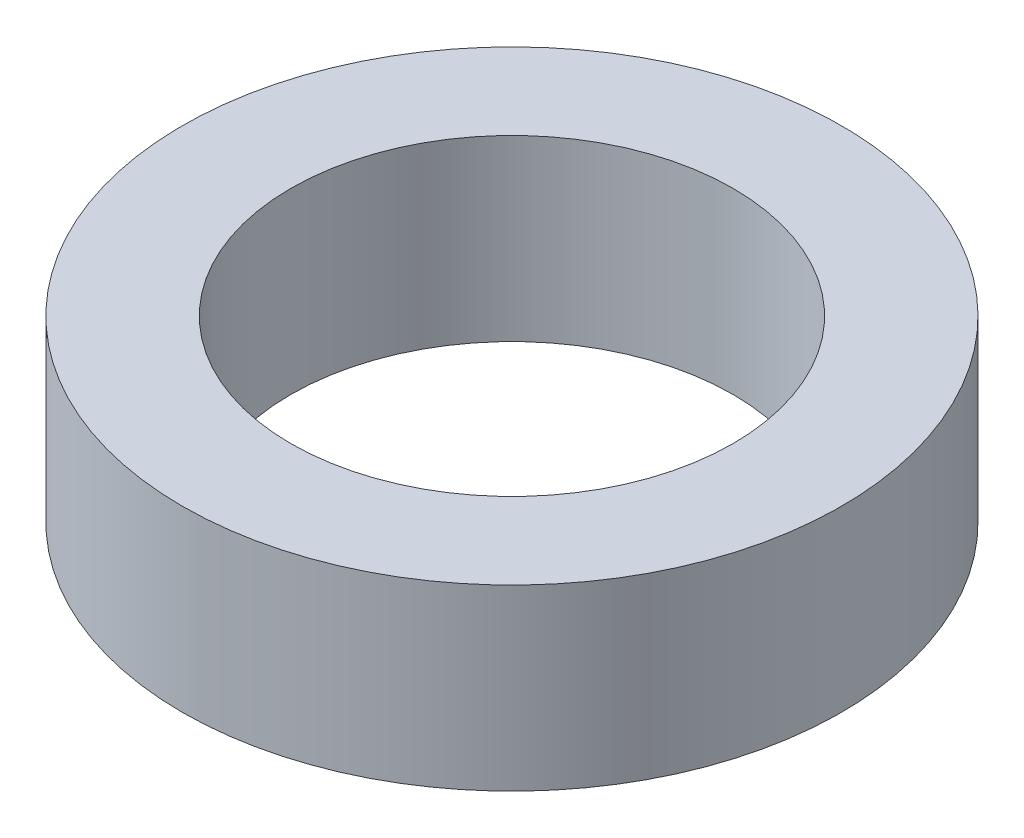
SolidWorks part; units mm, degrees
ref_plane "Front Plane" through (0, 0, 0) normal (0, 0, 1) x (1, 0, 0)
ref_plane "Top Plane" through (0, 0, 0) normal (0, 1, 0) x (1, 0, 0)
ref_plane "Right Plane" through (0, 0, 0) normal (1, 0, 0) x (0, 0, -1)
sketch "Sketch1" plane through (0, 0, 0) normal (0, 1, 0) x (1, 0, 0)
  circle A0 centre (0, 0) radius 4.025
  circle A1 centre (0, 0) radius 6
  dimension "D1" = 8.05
  dimension "D2" = 12
extrude "Boss-Extrude1" add sketch "Sketch1" along normal blind 3.25
